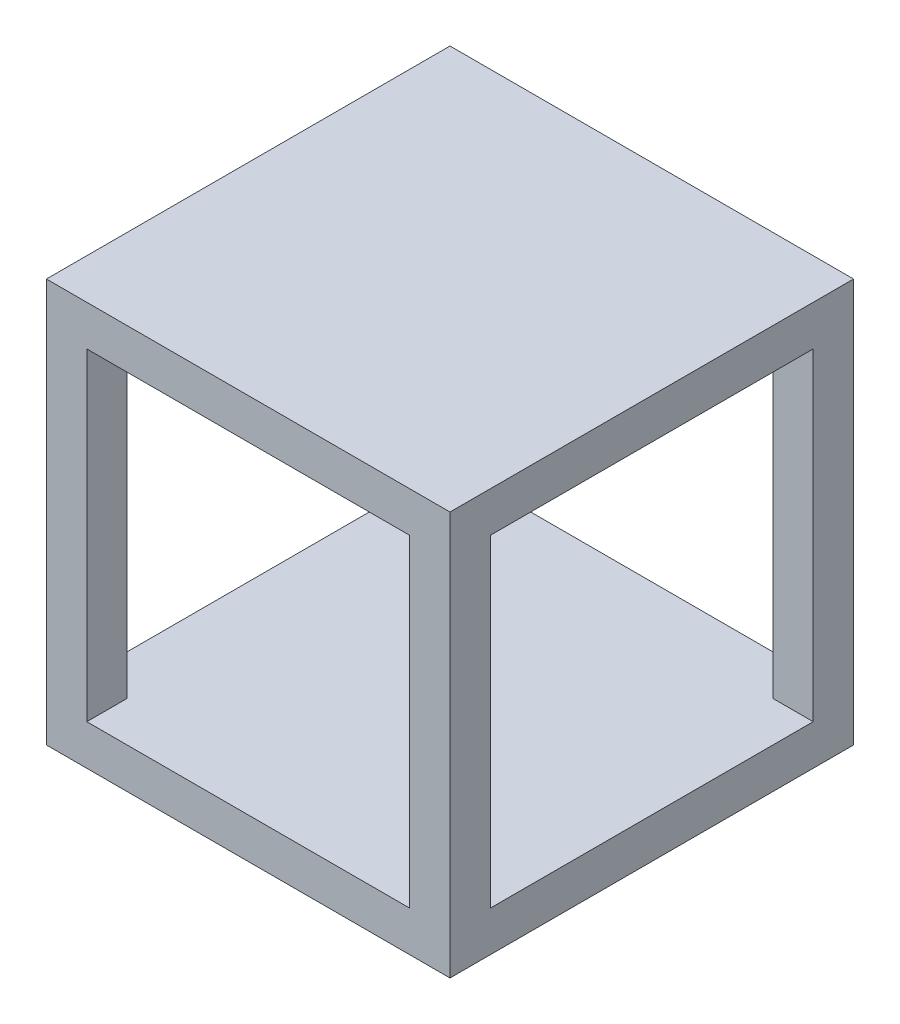
SolidWorks part; units mm, degrees
ref_plane "Front Plane" through (0, 0, 0) normal (0, 0, 1) x (1, 0, 0)
ref_plane "Top Plane" through (0, 0, 0) normal (0, 1, 0) x (1, 0, 0)
ref_plane "Right Plane" through (0, 0, 0) normal (1, 0, 0) x (0, 0, -1)
sketch "Sketch2" plane through (0, 0, 0) normal (0, 0, 1) x (1, 0, 0)
  line L1 (0, 0) -> (50, 0)
  line L2 (0, 0) -> (0, 50)
  line L3 (0, 50) -> (50, 50)
  line L4 (50, 0) -> (50, 50)
  dimension "D1" = 50
  dimension "D2" = 50
extrude "Boss-Extrude1" add sketch "Sketch2" along normal blind 50 contours L2 L1 L4 L3
sketch "Sketch3" plane through (0, 0, 50) normal (0, 0, 1) x (1, 0, 0)
  line L1 (0, 50) -> (5, 50)
  line L2 (0, 50) -> (0, 45)
  line L3 (0, 45) -> (5, 45)
  line L4 (5, 50) -> (5, 45)
  line L5 (50, 50) -> (45, 50)
  line L6 (50, 50) -> (50, 45)
  line L7 (50, 45) -> (45, 45)
  line L8 (45, 50) -> (45, 45)
  line L9 (0, 0) -> (5, 0)
  line L10 (0, 0) -> (0, 5)
  line L11 (0, 5) -> (5, 5)
  line L12 (5, 0) -> (5, 5)
  line L13 (50, 0) -> (45, 0)
  line L14 (50, 0) -> (50, 5)
  line L15 (50, 5) -> (45, 5)
  line L16 (45, 0) -> (45, 5)
  dimension "D1" = 5
  dimension "D2" = 5
  dimension "D3" = 5
  dimension "D4" = 5
  dimension "D5" = 5
  dimension "D6" = 5
  dimension "D7" = 5
  dimension "D8" = 5
sketch "Sketch4" plane through (0, 0, 50) normal (0, 0, 1) x (1, 0, 0)
  line L0 (50, 5) -> (45, 5) construction
  line L1 (5, 45) -> (45, 45)
  line L2 (5, 45) -> (5, 5)
  line L3 (5, 5) -> (45, 5)
  line L4 (45, 45) -> (45, 5)
  dimension "D1" = 40
extrude "Cut-Extrude1" cut sketch "Sketch4" against normal blind 50
sketch "Sketch7" plane through (0, 0, 0) normal (1, 0, 0) x (0, 0, -1)
  line L0 (-50, 45) -> (-45, 45)
  line L1 (-45, 50) -> (-45, 45)
  line L2 (-50, 50) -> (0, 50) construction
  line L4 (-45, 45) -> (-5, 45)
  line L5 (-45, 45) -> (-45, 5)
  line L6 (-45, 5) -> (-5, 5)
  line L7 (-5, 45) -> (-5, 5)
  dimension "D1" = 40
  dimension "D2" = 40
extrude "Cut-Extrude2" cut sketch "Sketch7" along normal blind 50 contours L7 L4 L5 L6
sketch "Sketch8" plane through (0, 0, 0) normal (0, 1, 0) x (1, 0, 0)
  line L0 (0, 0) -> (50, 0) construction
  line L1 (2.25, 0) -> (2.25, -2.25)
  line L2 (0, -2.25) -> (2.25, -2.25)
  line L3 (0, -27.5) -> (0, 27.5) construction
  line L4 (50, -47.75) -> (47.75, -47.75)
  line L5 (50, -50) -> (50, 0) construction
  line L6 (47.75, -47.75) -> (47.75, -50)
  line L7 (50, -50) -> (45, -50) construction
  line L8 (2.25, -4.5) -> (4.5, -4.5)
  line L9 (2.25, -2.25) -> (47.75, -2.25)
  line L10 (2.25, -2.25) -> (2.25, -47.75)
  line L11 (2.25, -47.75) -> (47.75, -47.75)
  line L12 (47.75, -2.25) -> (47.75, -47.75)
  line L13 (4.5, -2.25) -> (4.5, -4.5)
  line L14 (45.5635, -47.75) -> (45.5635, -45.4098)
  line L15 (45.5635, -45.4098) -> (47.8135, -45.4098)
  line L16 (47.8135, -45.4098) -> (45.5635, -45.4098)
  line L17 (2.25, -17.6586) -> (4.5, -17.6586)
  line L18 (4.5, -4.5) -> (45.5635, -4.5)
  line L19 (4.5, -4.5) -> (4.5, -45.4098)
  line L20 (4.5, -45.4098) -> (45.5635, -45.4098)
  line L21 (45.5635, -4.5) -> (45.5635, -45.4098)
  line L22 (4.5, -17.6586) -> (4.5, -15.4086)
  line L23 (2.25, -45.4098) -> (4.5, -45.4098)
  dimension "D1" = 2.25
sketch "Sketch10" plane through (0, 0, 0) normal (0, 1, 0) x (1, 0, 0)
  line L1 (4.5, -4.5) -> (45.5635, -4.5)
  line L2 (4.5, -4.5) -> (4.5, -45.4098)
  line L3 (4.5, -45.4098) -> (45.5635, -45.4098)
  line L4 (45.5635, -4.5) -> (45.5635, -45.4098)
  line L5 (47.75, -47.75) -> (2.25, -47.75)
  line L6 (47.75, -47.75) -> (47.75, -2.25)
  line L7 (47.75, -2.25) -> (2.25, -2.25)
  line L8 (2.25, -47.75) -> (2.25, -2.25)
extrude "Cut-Extrude3" cut sketch "Sketch10" along normal blind 2.5
sketch "Sketch6" plane through (0, 0, 0) normal (0, 0, 1) x (1, 0, 0)
